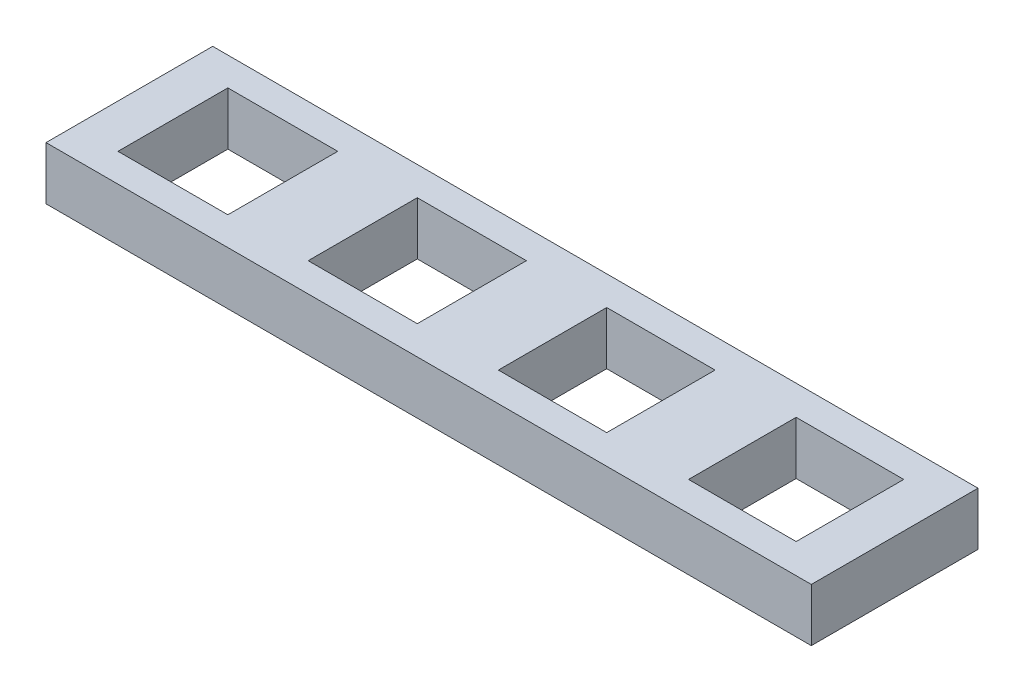
SolidWorks part; units mm, degrees
ref_plane "Front Plane" through (0, 0, 0) normal (0, 0, 1) x (1, 0, 0)
ref_plane "Top Plane" through (0, 0, 0) normal (0, 1, 0) x (1, 0, 0)
ref_plane "Right Plane" through (0, 0, 0) normal (1, 0, 0) x (0, 0, -1)
sketch "Sketch2" [suppressed] plane through (0, 0, 0) normal (0, 1, 0) x (1, 0, 0)
  line L0 (70, 25) -> (70, 0) construction
  line L1 (0, 0) -> (140, 0)
  line L2 (0, 0) -> (0, 25)
  line L3 (0, 25) -> (140, 25)
  line L4 (140, 0) -> (140, 25)
  line L5 (62.25, 20.25) -> (77.75, 20.25)
  line L6 (62.25, 20.25) -> (62.25, 4.75)
  line L7 (62.25, 4.75) -> (77.75, 4.75)
  line L8 (77.75, 20.25) -> (77.75, 4.75)
  line L9 (62.25, 20.25) -> (77.75, 4.75) construction
  line L10 (62.25, 4.75) -> (77.75, 20.25) construction
  line L11 (0, 12.5) -> (140, 12.5) construction
  line L12 (87.25, 20.25) -> (87.25, 4.75) construction
  line L13 (87.25, 20.25) -> (102.75, 20.25) construction
  line L14 (102.75, 20.25) -> (102.75, 4.75) construction
  line L15 (87.25, 4.75) -> (102.75, 4.75) construction
  line L16 (112.25, 20.25) -> (112.25, 4.75) construction
  line L17 (112.25, 20.25) -> (127.75, 20.25) construction
  line L18 (127.75, 20.25) -> (127.75, 4.75) construction
  line L19 (112.25, 4.75) -> (127.75, 4.75) construction
  line L20 (62.25, 20.25) -> (62.25, 4.75)
  line L21 (62.25, 20.25) -> (77.75, 20.25)
  line L22 (77.75, 20.25) -> (77.75, 4.75)
  line L23 (62.25, 4.75) -> (77.75, 4.75)
  line L24 (87.25, 20.25) -> (87.25, 4.75) construction
  line L25 (87.25, 20.25) -> (102.75, 20.25) construction
  line L26 (102.75, 20.25) -> (102.75, 4.75) construction
  line L27 (87.25, 4.75) -> (102.75, 4.75) construction
  line L28 (37.25, 20.25) -> (37.25, 4.75) construction
  line L29 (37.25, 20.25) -> (52.75, 20.25) construction
  line L30 (52.75, 20.25) -> (52.75, 4.75) construction
  line L31 (37.25, 4.75) -> (52.75, 4.75) construction
  line L32 (62.25, 20.25) -> (62.25, 4.75)
  line L33 (62.25, 20.25) -> (77.75, 20.25)
  line L34 (77.75, 20.25) -> (77.75, 4.75)
  line L35 (62.25, 4.75) -> (77.75, 4.75)
  line L36 (37.25, 20.25) -> (37.25, 4.75) construction
  line L37 (37.25, 20.25) -> (52.75, 20.25) construction
  line L38 (52.75, 20.25) -> (52.75, 4.75) construction
  line L39 (37.25, 4.75) -> (52.75, 4.75) construction
  line L40 (12.25, 20.25) -> (12.25, 4.75) construction
  line L41 (12.25, 20.25) -> (27.75, 20.25) construction
  line L42 (27.75, 20.25) -> (27.75, 4.75) construction
  line L43 (12.25, 4.75) -> (27.75, 4.75) construction
  line L44 (37.75, 19.75) -> (52.25, 19.75)
  line L45 (52.25, 19.75) -> (52.25, 5.25)
  line L46 (37.75, 5.25) -> (52.25, 5.25)
  line L47 (37.75, 19.75) -> (37.75, 5.25)
  line L48 (13.25, 19.25) -> (26.75, 19.25)
  line L49 (26.75, 19.25) -> (26.75, 5.75)
  line L50 (13.25, 5.75) -> (26.75, 5.75)
  line L51 (13.25, 19.25) -> (13.25, 5.75)
  line L52 (86.75, 20.75) -> (103.25, 20.75)
  line L53 (103.25, 20.75) -> (103.25, 4.25)
  line L54 (86.75, 4.25) -> (103.25, 4.25)
  line L55 (86.75, 20.75) -> (86.75, 4.25)
  line L56 (111.25, 21.25) -> (128.75, 21.25)
  line L57 (128.75, 21.25) -> (128.75, 3.75)
  line L58 (111.25, 3.75) -> (128.75, 3.75)
  line L59 (111.25, 21.25) -> (111.25, 3.75)
  point P5 (70, 12.5)
  dimension "D1" = 140
  dimension "D2" = 25
  dimension "D3" = 15.5
  dimension "D4" = 15.5
  dimension "D5" = 3
  dimension "D6" = 3
  dimension "D7" = 0.5
  dimension "D8" = 1
  dimension "D9" = 0.5
  dimension "D10" = 1
extrude "Boss-Extrude4" [suppressed] add sketch "Sketch2" along normal blind 5 contours L2 L1 L4 L3 | L48 L49 L50 L51 | L44 L45 L46 L47 | L52 L53 L54 L55 | L56 L57 L58 L59 | L20 L23 L22 L21
sketch "Sketch3" plane through (0, 0, 0) normal (0, 1, 0) x (1, 0, 0)
  line L0 (13, 18.25) -> (13, 3.75) construction
  line L9 (0, 0) -> (101, 0)
  line L10 (0, 0) -> (0, 22)
  line L11 (0, 22) -> (101, 22)
  line L12 (101, 0) -> (101, 22)
  line L13 (5.75, 18.25) -> (20.25, 18.25)
  line L14 (5.75, 18.25) -> (5.75, 3.75)
  line L15 (5.75, 3.75) -> (20.25, 3.75)
  line L16 (20.25, 18.25) -> (20.25, 3.75)
  line L21 (38, 18.25) -> (38, 3.75) construction
  line L26 (63, 18.25) -> (63, 3.75) construction
  line L27 (30.75, 18.25) -> (45.25, 18.25) construction
  line L28 (45.25, 18.25) -> (45.25, 3.75) construction
  line L29 (30.75, 3.75) -> (45.25, 3.75) construction
  line L30 (30.75, 18.25) -> (30.75, 3.75) construction
  line L31 (55.75, 18.25) -> (70.25, 18.25) construction
  line L32 (70.25, 18.25) -> (70.25, 3.75) construction
  line L33 (55.75, 3.75) -> (70.25, 3.75) construction
  line L34 (55.75, 18.25) -> (55.75, 3.75) construction
  line L36 (30.8, 3.8) -> (45.2, 3.8)
  line L37 (30.8, 3.8) -> (30.8, 18.2)
  line L38 (30.8, 18.2) -> (45.2, 18.2)
  line L39 (45.2, 3.8) -> (45.2, 18.2)
  line L40 (30.8, 3.8) -> (45.2, 18.2) construction
  line L41 (30.8, 18.2) -> (45.2, 3.8) construction
  line L42 (55.85, 3.85) -> (70.15, 3.85)
  line L43 (55.85, 3.85) -> (55.85, 18.15)
  line L44 (55.85, 18.15) -> (70.15, 18.15)
  line L45 (70.15, 3.85) -> (70.15, 18.15)
  line L46 (55.85, 3.85) -> (70.15, 18.15) construction
  line L47 (55.85, 18.15) -> (70.15, 3.85) construction
  line L51 (88, 18.25) -> (88, 3.75) construction
  line L52 (80.75, 18.25) -> (95.25, 18.25)
  line L53 (95.25, 18.25) -> (95.25, 3.75)
  line L54 (80.75, 3.75) -> (95.25, 3.75)
  line L55 (80.75, 18.25) -> (80.75, 3.75)
  line L57 (80.9, 3.9) -> (95.1, 3.9)
  line L58 (80.9, 3.9) -> (80.9, 18.1)
  line L59 (80.9, 18.1) -> (95.1, 18.1)
  line L60 (95.1, 3.9) -> (95.1, 18.1)
  line L61 (80.9, 3.9) -> (95.1, 18.1) construction
  line L62 (80.9, 18.1) -> (95.1, 3.9) construction
  point P10 (13, 11)
  point P11 (38, 11)
  point P12 (63, 11)
  point P13 (38, 11)
  point P21 (63, 11)
  point P44 (88, 11)
  dimension "D1" = 101
  dimension "D2" = 22
  dimension "D3" = 14.5
  dimension "D4" = 13
  dimension "D5" = 11
  dimension "D7" = 25
  dimension "D8" = 25
  dimension "D9" = 14.4
  dimension "D10" = 14.3
  dimension "D11" = 14.2
  dimension "D6" = 4
extrude "Boss-Extrude5" add sketch "Sketch3" along normal blind 7
